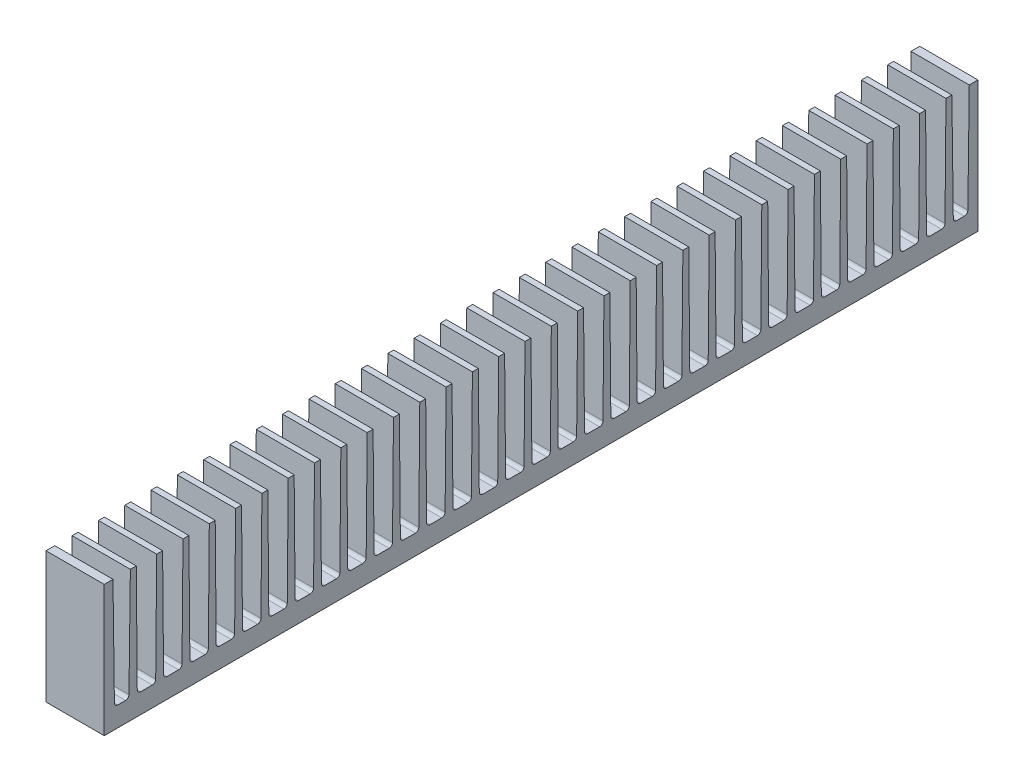
SolidWorks part; units mm, degrees
ref_plane "Front" through (0, 0, 0) normal (0, 0, 1) x (1, 0, 0)
ref_plane "Top" through (0, 0, 0) normal (0, 1, 0) x (1, 0, 0)
ref_plane "Right" through (0, 0, 0) normal (1, 0, 0) x (0, 0, -1)
sketch "Sketch1" plane through (0, 0, 0) normal (1, 0, 0) x (0, 0, -1)
  line L0 (0, 25.7386) -> (0, 0) construction
  line L1 (-45, 6.75) -> (45, 6.75)
  line L2 (-45, 6.75) -> (-45, -6.75)
  line L3 (-45, -6.75) -> (45, -6.75)
  line L4 (45, 6.75) -> (45, -6.75)
  line L5 (0, 0) -> (29.6591, 0) construction
  dimension "D1" = 90
  dimension "D2" = 13.5
extrude "Boss-Extrude1" add sketch "Sketch1" along normal mid plane 6
sketch "Sketch2" plane through (3, 0, 0) normal (1, 0, 0) x (0, 0, -1)
  line L0 (-44.1, 6.75) -> (-43.955, -4.3546)
  line L1 (45, 6.75) -> (-45, 6.75) construction
  line L2 (-43.605, -4.7) -> (-42.805, -4.7)
  line L3 (-42.455, -4.3546) -> (-42.31, 6.75)
  line L4 (-42.31, 6.75) -> (-44.1, 6.75)
  line L5 (-43.205, 6.75) -> (-43.205, -4.7) construction
  line L6 (-45, 6.75) -> (-45, -6.75) construction
  arc A0 (-43.955, -4.3546) -> (-43.605, -4.7) centre (-43.605, -4.35) ccw
  arc A1 (-42.805, -4.7) -> (-42.455, -4.3546) centre (-42.805, -4.35) ccw
  dimension "D5" = 0.35
  dimension "D1" = 0.9
  dimension "D2" = 1.79
  dimension "D3" = 11.45
  dimension "D4" = 1.5
extrude "Cut-Extrude1" cut sketch "Sketch2" against normal up to next (6 mm away)
sketch "Sketch3" plane through (3, 0, 0) normal (1, 0, 0) x (0, 0, -1)
  line L0 (-41.7, 6.75) -> (-39.6, 6.75)
  line L1 (45, 6.75) -> (-42.31, 6.75) construction
  line L2 (-39.6, 6.75) -> (-39.7, -4.3532)
  line L3 (-40.05, -4.7) -> (-41.25, -4.7)
  line L4 (-41.6, -4.3532) -> (-41.7, 6.75)
  line L5 (-40.65, 6.75) -> (-40.65, -4.7) construction
  line L6 (-43.605, -4.7) -> (-42.805, -4.7) construction
  arc A0 (-39.7, -4.3532) -> (-40.05, -4.7) centre (-40.05, -4.35) cw
  arc A1 (-41.25, -4.7) -> (-41.6, -4.3532) centre (-41.25, -4.35) cw
  arc A2 (-42.805, -4.7) -> (-42.455, -4.3546) centre (-42.805, -4.35) ccw construction
  dimension "D1" = 2.1
  dimension "D2" = 0.61
  dimension "D3" = 1.9
extrude "Cut-Extrude2" cut sketch "Sketch3" against normal up to next (6 mm away)
mirror "Mirror1" about plane through (0, 0, 0) normal (0, 0, 1) of "Cut-Extrude1"
pattern_linear "LPattern1" count 31 spacing 2.71 along (0, 0, -1) of "Cut-Extrude2"
